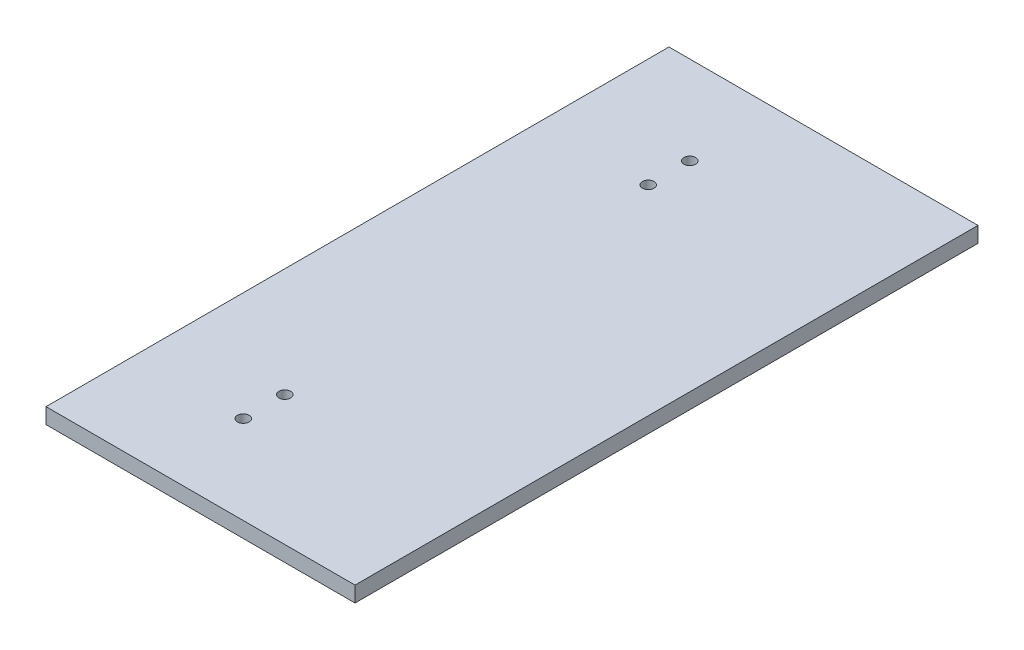
SolidWorks part; units mm, degrees
ref_plane "Front Plane" through (0, 0, 0) normal (0, 0, 1) x (1, 0, 0)
ref_plane "Top Plane" through (0, 0, 0) normal (0, 1, 0) x (1, 0, 0)
ref_plane "Right Plane" through (0, 0, 0) normal (1, 0, 0) x (0, 0, -1)
sketch "Sketch1" plane through (0, 0, 0) normal (0, 1, 0) x (1, 0, 0)
  line L0 (-189.8801, 78.6262) -> (-291.4801, 78.6262) construction
  line L1 (-329.5801, 218.3262) -> (-77.5801, 218.3262)
  line L2 (-329.5801, 218.3262) -> (-329.5801, -289.6738)
  line L3 (-329.5801, -289.6738) -> (-77.5801, -289.6738)
  line L4 (-77.5801, 218.3262) -> (-77.5801, -289.6738)
  line L5 (-291.4801, -251.5738) -> (-189.8801, -251.5738) construction
  line L6 (-189.8801, -251.5738) -> (-189.8801, -149.9738) construction
  line L7 (-189.8801, -149.9738) -> (-291.4801, -149.9738) construction
  line L8 (-291.4801, -149.9738) -> (-291.4801, -251.5738) construction
  line L9 (-291.4801, 180.2262) -> (-189.8801, 180.2262) construction
  line L10 (-189.8801, 180.2262) -> (-189.8801, 78.6262) construction
  line L11 (-291.4801, 180.2262) -> (-291.4801, 78.6262) construction
  line L12 (-240.6801, 180.2262) -> (-240.6801, 78.6262) construction
  line L13 (-235.6314, 180.2262) -> (-235.6314, 146.3595) construction
  line L14 (-235.6314, 78.6262) -> (-235.6314, 112.4928) construction
  line L15 (-240.6801, -149.9738) -> (-240.6801, -251.5738) construction
  line L16 (-235.2176, -251.5738) -> (-235.2176, -217.7072) construction
  line L17 (-235.2176, -149.9738) -> (-235.2176, -183.8405) construction
  circle A0 centre (-240.6801, 112.4928) radius 4.7625
  circle A1 centre (-240.6801, 146.3595) radius 4.7625
  circle A2 centre (-240.6801, -183.8405) radius 4.7625
  circle A3 centre (-240.6801, -217.7072) radius 4.7625
  dimension "D11" = 71.9667
  dimension "D1" = 508
  dimension "D2" = 252
  dimension "D3" = 38.1
  dimension "D4" = 38.1
  dimension "D5" = 101.6
  dimension "D6" = 101.6
  dimension "D7" = 101.6
  dimension "D8" = 101.6
  dimension "D9" = 38.1
  dimension "D10" = 38.1
  dimension "D12" = 88.9
extrude "Boss-Extrude4" add sketch "Sketch1" along normal blind 12.7
